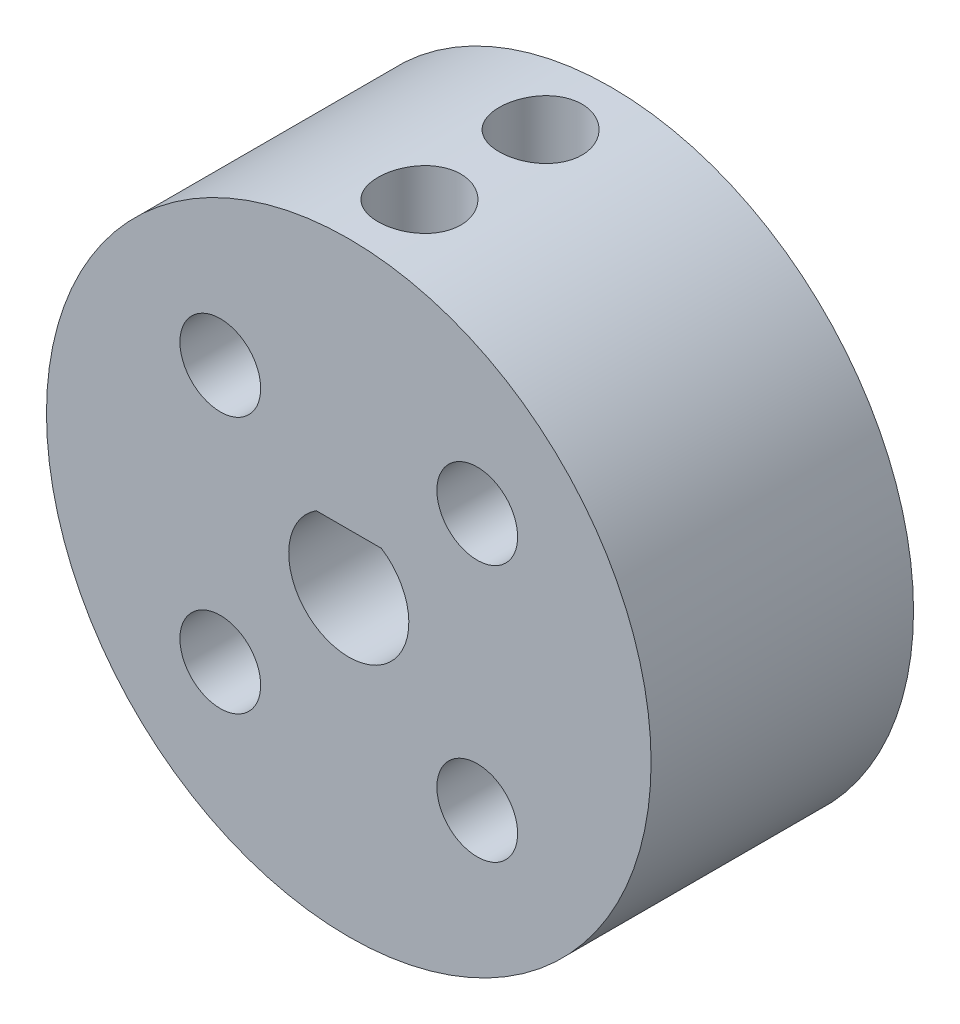
SolidWorks part; units mm, degrees
ref_plane "Front" through (0, 0, 0) normal (0, 0, 1) x (1, 0, 0)
ref_plane "Top" through (0, 0, 0) normal (0, 1, 0) x (1, 0, 0)
ref_plane "Right" through (0, 0, 0) normal (1, 0, 0) x (0, 0, -1)
sketch "Sketch1" plane through (0, 0, 0) normal (0, 0, 1) x (1, 0, 0)
  line L0 (1.6126, 2.5) -> (-1.6126, 2.5)
  arc A0 (-1.6126, 2.5) -> (1.6126, 2.5) centre (0, 0) ccw
  circle A1 centre (0, 0) radius 14.975
  circle A2 centre (0, 0) radius 2.975 construction
  dimension "D1" = 5.95
  dimension "D3" = 2.5
  dimension "D2" = 12
extrude "Boss-Extrude1" add sketch "Sketch1" along normal blind 13
sketch "Sketch3" plane through (0, 0, 0) normal (0, 1, 0) x (1, 0, 0)
  circle A0 centre (0, -3.5) radius 2.05
  circle A1 centre (0, -9.5) radius 2.05
  dimension "D1" = 4.1
  dimension "D3" = 4.1
  dimension "D2" = 3.5
  dimension "D4" = 6
extrude "Cut-Extrude2" cut sketch "Sketch3" along normal blind 16
sketch "Sketch11" plane through (0, 0, 0) normal (0, 0, -1) x (-1, 0, 0)
  line L0 (0, 0) -> (-6.364, 6.364) construction
  line L1 (-6.364, 2.3802) -> (-2.914, 4.3721)
  line L2 (-2.914, 4.3721) -> (-2.914, 8.3558)
  line L3 (-2.914, 8.3558) -> (-6.364, 10.3477)
  line L4 (-6.364, 10.3477) -> (-9.814, 8.3558)
  line L5 (-9.814, 8.3558) -> (-9.814, 4.3721)
  line L6 (-9.814, 4.3721) -> (-6.364, 2.3802)
  line L7 (0, 0) -> (0, 14.975) construction
  line L8 (0, 0) -> (6.364, 6.364) construction
  line L12 (9.814, 8.3558) -> (6.364, 10.3477)
  line L13 (6.364, 10.3477) -> (2.914, 8.3558)
  line L14 (2.914, 8.3558) -> (2.914, 4.3721)
  line L15 (2.914, 4.3721) -> (6.364, 2.3802)
  line L16 (6.364, 2.3802) -> (9.814, 4.3721)
  line L17 (9.814, 4.3721) -> (9.814, 8.3558)
  line L18 (0, 0) -> (2.336, 0) construction
  line L20 (0, 0) -> (-6.364, 6.364) construction
  line L21 (0, 0) -> (6.364, 6.364) construction
  line L22 (0, 0) -> (6.364, -6.364) construction
  line L23 (0, 0) -> (-6.364, -6.364) construction
  line L24 (9.814, -4.3721) -> (9.814, -8.3558)
  line L25 (6.364, -2.3802) -> (9.814, -4.3721)
  line L26 (2.914, -4.3721) -> (6.364, -2.3802)
  line L27 (2.914, -8.3558) -> (2.914, -4.3721)
  line L28 (6.364, -10.3477) -> (2.914, -8.3558)
  line L29 (9.814, -8.3558) -> (6.364, -10.3477)
  line L30 (-9.814, -4.3721) -> (-6.364, -2.3802)
  line L31 (-9.814, -8.3558) -> (-9.814, -4.3721)
  line L32 (-6.364, -10.3477) -> (-9.814, -8.3558)
  line L33 (-2.914, -8.3558) -> (-6.364, -10.3477)
  line L34 (-2.914, -4.3721) -> (-2.914, -8.3558)
  line L35 (-6.364, -2.3802) -> (-2.914, -4.3721)
  line L36 (0, 0) -> (-6.364, -6.364) construction
  line L37 (0, 0) -> (6.364, -6.364) construction
  circle A0 centre (-6.364, 6.364) radius 3.45 construction
  circle A1 centre (0, 0) radius 14.975 construction
  circle A2 centre (6.364, 6.364) radius 3.45 construction
  circle A3 centre (6.364, -6.364) radius 3.45 construction
  circle A4 centre (-6.364, -6.364) radius 3.45 construction
  point P20 (0, 0)
  point P35 (0, 0)
  dimension "D1" = 6.9
  dimension "D2" = 45
  dimension "D3" = 9
  dimension "D4" = 4
  dimension "D5" = 6.9
extrude "Cut-Extrude7" cut sketch "Sketch11" against normal blind 5
sketch "Sketch12" plane through (0, 0, 5) normal (0, 0, -1) x (-1, 0, 0)
  line L0 (0, 0) -> (-6.364, 6.364) construction
  line L1 (0, 0) -> (0, 14.975) construction
  circle A0 centre (-6.364, 6.364) radius 2
  circle A1 centre (0, 0) radius 14.975 construction
  circle A2 centre (6.364, 6.364) radius 2
  circle A3 centre (6.364, -6.364) radius 2
  circle A4 centre (-6.364, -6.364) radius 2
  point P16 (0, 0)
  dimension "D1" = 45
  dimension "D3" = 4
  dimension "D2" = 9
  dimension "D4" = 4
extrude "Cut-Extrude8" cut sketch "Sketch12" against normal through all
sketch "Sketch13" plane through (0, 0, 0) normal (0, 0, -1) x (-1, 0, 0)
  circle A0 centre (0, 0) radius 2.975
  dimension "D1" = 5.95
extrude "Cut-Extrude9" cut sketch "Sketch13" against normal blind 1
